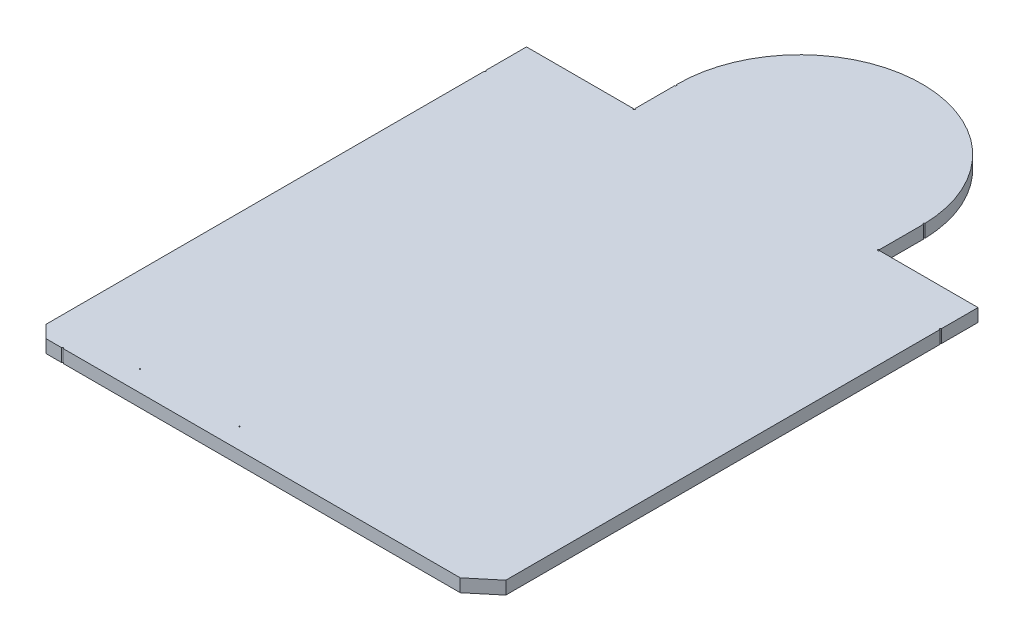
SolidWorks part; units mm, degrees
ref_plane "Front Plane" through (0, 0, 0) normal (0, 0, 1) x (1, 0, 0)
ref_plane "Top Plane" through (0, 0, 0) normal (0, 1, 0) x (1, 0, 0)
ref_plane "Right Plane" through (0, 0, 0) normal (1, 0, 0) x (0, 0, -1)
ref_plane "Plane1" through (0, 30.5392, 0) normal (0, 1, 0) x (1, 0, 0)
ref_plane "Plane2" through (0, 30.5392, 0) normal (0, -1, 0) x (-1, 0, 0)
sketch "Sketch3" plane through (0, 30.5392, 0) normal (0, 1, 0) x (1, 0, 0)
  line L0 (46.803, -39.9449) -> (46.803, -93.2849)
  line L1 (46.803, -93.2849) -> (43.755, -95.8249)
  line L2 (43.755, -95.8249) -> (-5.013, -95.8249)
  line L3 (-5.013, -95.8249) -> (-7.045, -95.8249)
  line L4 (-7.045, -95.8249) -> (-8.569, -94.3009)
  line L5 (-8.569, -40.4529) -> (-8.569, -94.3009)
  line L6 (-8.569, -40.4529) -> (-8.569, -35.3729)
  line L7 (-8.569, -35.3729) -> (4.639, -35.3729)
  line L8 (34.611, -35.3729) -> (46.803, -35.3729)
  line L9 (46.803, -35.3729) -> (46.803, -39.9449)
  line L10 (4.639, -35.3729) -> (4.639, -30.2929)
  line L11 (34.611, -35.3729) -> (34.611, -29.7849)
  line L12 (8.3601, -30.2865) -> (30.3819, -30.2992) construction
  line L13 (8.3601, -31.2454) -> (10.0619, -31.2454) construction
  line L14 (8.3601, -31.2454) -> (8.3601, -29.3277) construction
  line L15 (8.3601, -29.3277) -> (10.0619, -29.3277) construction
  line L16 (10.0619, -31.2454) -> (10.0619, -29.3277) construction
  line L17 (18.4185, -19.3582) -> (20.3362, -19.3582) construction
  line L18 (18.4185, -19.3582) -> (18.4185, -20.9838) construction
  line L19 (18.4185, -20.9838) -> (20.3362, -20.9838) construction
  line L20 (20.3362, -19.3582) -> (20.3362, -20.9838) construction
  line L21 (28.7182, -29.3404) -> (30.3819, -29.3404) construction
  line L22 (28.7182, -29.3404) -> (28.7182, -31.2581) construction
  line L23 (28.7182, -31.2581) -> (30.3819, -31.2581) construction
  line L24 (30.3819, -29.3404) -> (30.3819, -31.2581) construction
  line L25 (19.3774, -19.3582) -> (19.371, -30.2929) construction
  line L26 (40.907, -33.9184) -> (8.141, -33.9184) construction
  line L27 (8.141, -33.9184) -> (5.601, -36.4584) construction
  line L28 (5.601, -36.4584) -> (-7.353, -36.4584) construction
  line L29 (-7.353, -36.4584) -> (-7.353, -102.4984) construction
  line L30 (43.447, -36.4584) -> (40.907, -33.9184) construction
  line L31 (45.987, -36.4584) -> (43.447, -36.4584) construction
  line L32 (45.987, -102.4984) -> (45.987, -36.4584) construction
  line L33 (-7.353, -102.4984) -> (45.987, -102.4984) construction
  line L34 (-5.013, -93.2849) -> (1.947, -93.2849) construction
  line L35 (1.947, -93.2849) -> (14.147, -93.2849) construction
  line L36 (14.147, -93.2849) -> (43.247, -93.2849) construction
  line L37 (43.247, -93.2849) -> (45.787, -90.7449) construction
  line L38 (45.787, -36.1349) -> (43.247, -36.1349) construction
  line L39 (43.247, -36.1349) -> (40.707, -33.5949) construction
  line L40 (-7.553, -37.4049) -> (-7.553, -90.7449) construction
  line L41 (-7.553, -90.7449) -> (-5.013, -93.2849) construction
  line L42 (40.707, -33.5949) -> (7.687, -33.5949) construction
  line L43 (7.687, -33.5949) -> (5.147, -36.1349) construction
  line L44 (5.147, -36.1349) -> (-6.283, -36.1349) construction
  line L45 (-6.283, -36.1349) -> (-7.553, -37.4049) construction
  line L46 (45.787, -90.7449) -> (45.787, -36.1349) construction
  line L47 (1.947, -108.7849) -> (14.147, -108.7849) construction
  line L48 (32.647, -103.5849) -> (41.647, -103.5849) construction
  line L49 (1.947, -108.7849) -> (1.947, -93.2849) construction
  line L50 (14.147, -108.7849) -> (14.147, -93.2849) construction
  line L51 (32.647, -103.5849) -> (32.647, -93.3849) construction
  line L52 (41.647, -103.5849) -> (41.647, -93.3849) construction
  line L53 (40.907, -33.9184) -> (8.141, -33.9184) construction
  line L54 (8.141, -33.9184) -> (5.601, -36.4584) construction
  line L55 (5.601, -36.4584) -> (-7.353, -36.4584) construction
  line L56 (-7.353, -36.4584) -> (-7.353, -102.4984) construction
  line L57 (43.447, -36.4584) -> (40.907, -33.9184) construction
  line L58 (45.987, -36.4584) -> (43.447, -36.4584) construction
  line L59 (45.987, -102.4984) -> (45.987, -36.4584) construction
  line L60 (-7.353, -102.4984) -> (45.987, -102.4984) construction
  line L61 (1.947, -108.2884) -> (1.947, -92.9084) construction
  line L62 (13.527, -108.8484) -> (2.407, -108.8484) construction
  line L63 (13.987, -92.9084) -> (13.987, -108.2884) construction
  line L64 (1.947, -108.2884) -> (1.947, -92.9084)
  line L65 (13.527, -108.8484) -> (2.407, -108.8484)
  line L66 (13.987, -92.9084) -> (13.987, -108.2884)
  arc A0 (46.7014, -93.2849) -> (46.9046, -93.2849) centre (46.803, -93.2849) ccw
  arc A1 (46.9046, -39.9449) -> (46.7014, -39.9449) centre (46.803, -39.9449) ccw
  arc A2 (43.69, -95.7468) -> (43.8201, -95.9029) centre (43.755, -95.8249) ccw
  arc A3 (46.8681, -93.3629) -> (46.738, -93.2068) centre (46.803, -93.2849) ccw
  arc A4 (-5.013, -95.7233) -> (-5.013, -95.9265) centre (-5.013, -95.8249) ccw
  arc A5 (43.755, -95.9265) -> (43.755, -95.7233) centre (43.755, -95.8249) ccw
  arc A6 (-7.045, -95.7233) -> (-7.045, -95.9265) centre (-7.045, -95.8249) ccw
  arc A7 (-5.013, -95.9265) -> (-5.013, -95.7233) centre (-5.013, -95.8249) ccw
  arc A8 (-8.4971, -94.229) -> (-8.6408, -94.3727) centre (-8.569, -94.3009) ccw
  arc A9 (-7.1168, -95.8967) -> (-6.9731, -95.753) centre (-7.045, -95.8249) ccw
  arc A10 (-8.6706, -94.3009) -> (-8.4674, -94.3009) centre (-8.569, -94.3009) ccw
  arc A11 (-8.4674, -40.4529) -> (-8.6706, -40.4529) centre (-8.569, -40.4529) ccw
  arc A12 (-8.4674, -35.3729) -> (-8.6706, -35.3729) centre (-8.569, -35.3729) ccw
  arc A13 (-8.6706, -40.4529) -> (-8.4674, -40.4529) centre (-8.569, -40.4529) ccw
  arc A14 (4.639, -35.4745) -> (4.639, -35.2713) centre (4.639, -35.3729) ccw
  arc A15 (-8.569, -35.2713) -> (-8.569, -35.4745) centre (-8.569, -35.3729) ccw
  arc A16 (46.803, -35.4745) -> (46.803, -35.2713) centre (46.803, -35.3729) ccw
  arc A17 (34.611, -35.2713) -> (34.611, -35.4745) centre (34.611, -35.3729) ccw
  arc A18 (46.7014, -39.9449) -> (46.9046, -39.9449) centre (46.803, -39.9449) ccw
  arc A19 (46.9046, -35.3729) -> (46.7014, -35.3729) centre (46.803, -35.3729) ccw
  arc A20 (4.7406, -30.2911) -> (4.5374, -30.2929) centre (4.639, -30.292) ccw
  arc A21 (4.5374, -35.3729) -> (4.7406, -35.3729) centre (4.639, -35.3729) ccw
  arc A22 (34.7126, -29.7831) -> (34.5094, -29.7849) centre (34.611, -29.784) ccw
  arc A23 (34.5094, -35.3729) -> (34.7126, -35.3729) centre (34.611, -35.3729) ccw
  arc A24 (34.611, -29.7849) -> (4.639, -30.2929) centre (19.625, -30.0389) ccw
  arc A25 (34.5094, -29.7849) -> (34.7126, -29.7831) centre (34.611, -29.784) ccw
  arc A26 (4.5374, -30.2929) -> (4.7406, -30.2911) centre (4.639, -30.292) ccw
  circle A27 centre (19.371, -30.2929) radius 1.8649 construction
  arc A32 (8.4363, -29.3277) -> (8.3601, -29.3277) centre (8.3982, -29.3277) ccw construction
  arc A33 (8.3601, -31.2454) -> (8.4363, -31.2454) centre (8.3982, -31.2454) ccw construction
  arc A34 (10.0619, -29.3277) -> (9.9857, -29.3277) centre (10.0238, -29.3277) ccw construction
  arc A35 (9.9857, -31.2454) -> (10.0619, -31.2454) centre (10.0238, -31.2454) ccw construction
  arc A40 (30.3057, -31.2581) -> (30.3819, -31.2581) centre (30.3438, -31.2581) ccw construction
  arc A41 (30.3819, -29.3404) -> (30.3057, -29.3404) centre (30.3438, -29.3404) ccw construction
  arc A42 (28.6801, -31.2581) -> (28.7563, -31.2581) centre (28.7182, -31.2581) ccw construction
  arc A43 (28.7563, -29.3404) -> (28.6801, -29.3404) centre (28.7182, -29.3404) ccw construction
  arc A44 (20.3362, -19.3582) -> (20.3362, -19.282) centre (20.3362, -19.3201) ccw construction
  arc A45 (18.4185, -19.282) -> (18.4185, -19.3582) centre (18.4185, -19.3201) ccw construction
  arc A46 (20.3362, -20.9838) -> (20.3362, -20.9076) centre (20.3362, -20.9457) ccw construction
  arc A47 (18.4185, -20.9076) -> (18.4185, -20.9838) centre (18.4185, -20.9457) ccw construction
  arc A72 (1.947, -93.3484) -> (1.947, -93.2214) centre (1.947, -93.2849) ccw
  arc A73 (-5.013, -93.2214) -> (-5.013, -93.3484) centre (-5.013, -93.2849) ccw
  arc A74 (14.147, -93.3484) -> (14.147, -93.2214) centre (14.147, -93.2849) ccw
  arc A75 (1.947, -93.2214) -> (1.947, -93.3484) centre (1.947, -93.2849) ccw
  arc A76 (43.247, -93.3484) -> (43.247, -93.2214) centre (43.247, -93.2849) ccw
  arc A77 (14.147, -93.2214) -> (14.147, -93.3484) centre (14.147, -93.2849) ccw
  arc A78 (45.8319, -90.7898) -> (45.7421, -90.7) centre (45.787, -90.7449) ccw
  arc A79 (43.2021, -93.24) -> (43.2919, -93.3298) centre (43.247, -93.2849) ccw
  arc A80 (43.247, -36.0714) -> (43.247, -36.1984) centre (43.247, -36.1349) ccw
  arc A81 (45.787, -36.1984) -> (45.787, -36.0714) centre (45.787, -36.1349) ccw
  arc A82 (40.7519, -33.55) -> (40.6621, -33.6398) centre (40.707, -33.5949) ccw
  arc A83 (43.2021, -36.1798) -> (43.2919, -36.09) centre (43.247, -36.1349) ccw
  arc A84 (-7.6165, -90.7449) -> (-7.4895, -90.7449) centre (-7.553, -90.7449) ccw
  arc A85 (-7.4895, -37.4049) -> (-7.6165, -37.4049) centre (-7.553, -37.4049) ccw
  arc A86 (-5.0579, -93.3298) -> (-4.9681, -93.24) centre (-5.013, -93.2849) ccw
  arc A87 (-7.5081, -90.7) -> (-7.5979, -90.7898) centre (-7.553, -90.7449) ccw
  arc A88 (7.687, -33.5314) -> (7.687, -33.6584) centre (7.687, -33.5949) ccw
  arc A89 (40.707, -33.6584) -> (40.707, -33.5314) centre (40.707, -33.5949) ccw
  arc A90 (5.1021, -36.09) -> (5.1919, -36.1798) centre (5.147, -36.1349) ccw
  arc A91 (7.7319, -33.6398) -> (7.6421, -33.55) centre (7.687, -33.5949) ccw
  arc A92 (-6.283, -36.0714) -> (-6.283, -36.1984) centre (-6.283, -36.1349) ccw
  arc A93 (5.147, -36.1984) -> (5.147, -36.0714) centre (5.147, -36.1349) ccw
  arc A94 (-7.5979, -37.36) -> (-7.5081, -37.4498) centre (-7.553, -37.4049) ccw
  arc A95 (-6.2381, -36.1798) -> (-6.3279, -36.09) centre (-6.283, -36.1349) ccw
  arc A96 (45.8505, -36.1349) -> (45.7235, -36.1349) centre (45.787, -36.1349) ccw
  arc A97 (45.7235, -90.7449) -> (45.8505, -90.7449) centre (45.787, -90.7449) ccw
  arc A98 (14.147, -108.8484) -> (14.147, -108.7214) centre (14.147, -108.7849) ccw
  arc A99 (1.947, -108.7214) -> (1.947, -108.8484) centre (1.947, -108.7849) ccw
  arc A100 (41.647, -103.6484) -> (41.647, -103.5214) centre (41.647, -103.5849) ccw
  arc A101 (32.647, -103.5214) -> (32.647, -103.6484) centre (32.647, -103.5849) ccw
  arc A102 (2.0105, -93.2849) -> (1.8835, -93.2849) centre (1.947, -93.2849) ccw
  arc A103 (1.8835, -108.7849) -> (2.0105, -108.7849) centre (1.947, -108.7849) ccw
  arc A104 (14.2105, -93.2849) -> (14.0835, -93.2849) centre (14.147, -93.2849) ccw
  arc A105 (14.0835, -108.7849) -> (14.2105, -108.7849) centre (14.147, -108.7849) ccw
  arc A106 (32.7105, -93.3849) -> (32.5835, -93.3849) centre (32.647, -93.3849) ccw
  arc A107 (32.5835, -103.5849) -> (32.7105, -103.5849) centre (32.647, -103.5849) ccw
  arc A108 (41.7105, -93.3849) -> (41.5835, -93.3849) centre (41.647, -93.3849) ccw
  arc A109 (41.5835, -103.5849) -> (41.7105, -103.5849) centre (41.647, -103.5849) ccw
extrude "Boss-Extrude2" add sketch "Sketch3" along normal blind 1.5875
sketch "Sketch4" plane through (0, 32.1267, 0) normal (0, 1, 0) x (1, 0, 0)
  line L0 (8.3601, -29.7849) -> (30.3819, -29.7849) construction
  line L1 (8.3601, -30.7437) -> (10.0619, -30.7437) construction
  line L2 (8.3601, -30.7437) -> (8.3601, -28.826) construction
  line L3 (8.3601, -28.826) -> (10.0619, -28.826) construction
  line L4 (10.0619, -30.7437) -> (10.0619, -28.826) construction
  line L5 (18.4185, -18.8502) -> (20.3362, -18.8502) construction
  line L6 (18.4185, -18.8502) -> (18.4185, -20.4758) construction
  line L7 (18.4185, -20.4758) -> (20.3362, -20.4758) construction
  line L8 (20.3362, -18.8502) -> (20.3362, -20.4758) construction
  line L9 (28.7182, -28.826) -> (30.3819, -28.826) construction
  line L10 (28.7182, -28.826) -> (28.7182, -30.7437) construction
  line L11 (28.7182, -30.7437) -> (30.3819, -30.7437) construction
  line L12 (30.3819, -28.826) -> (30.3819, -30.7437) construction
  line L13 (19.3774, -18.8502) -> (19.371, -29.7849) construction
  arc A0 (34.611, -29.7849) -> (4.639, -29.7849) centre (19.625, -30.0389) ccw
  circle A1 centre (19.371, -29.7849) radius 1.8649 construction
  arc A2 (8.4363, -28.826) -> (8.3601, -28.826) centre (8.3982, -28.826) ccw construction
  arc A3 (8.3601, -30.7437) -> (8.4363, -30.7437) centre (8.3982, -30.7437) ccw construction
  arc A4 (10.0619, -28.826) -> (9.9857, -28.826) centre (10.0238, -28.826) ccw construction
  arc A5 (9.9857, -30.7437) -> (10.0619, -30.7437) centre (10.0238, -30.7437) ccw construction
  arc A6 (30.3057, -30.7437) -> (30.3819, -30.7437) centre (30.3438, -30.7437) ccw construction
  arc A7 (30.3819, -28.826) -> (30.3057, -28.826) centre (30.3438, -28.826) ccw construction
  arc A8 (28.6801, -30.7437) -> (28.7563, -30.7437) centre (28.7182, -30.7437) ccw construction
  arc A9 (28.7563, -28.826) -> (28.6801, -28.826) centre (28.7182, -28.826) ccw construction
  arc A10 (20.3362, -18.8502) -> (20.3362, -18.774) centre (20.3362, -18.8121) ccw construction
  arc A11 (18.4185, -18.774) -> (18.4185, -18.8502) centre (18.4185, -18.8121) ccw construction
  arc A12 (20.3362, -20.4758) -> (20.3362, -20.3996) centre (20.3362, -20.4377) ccw construction
  arc A13 (18.4185, -20.3996) -> (18.4185, -20.4758) centre (18.4185, -20.4377) ccw construction
  arc A14 (34.6089, -29.6824) -> (4.6376, -30.1904) centre (19.625, -30.0389) ccw construction
  arc A15 (34.6089, -29.6824) -> (4.6376, -30.1904) centre (19.625, -30.0389) ccw
